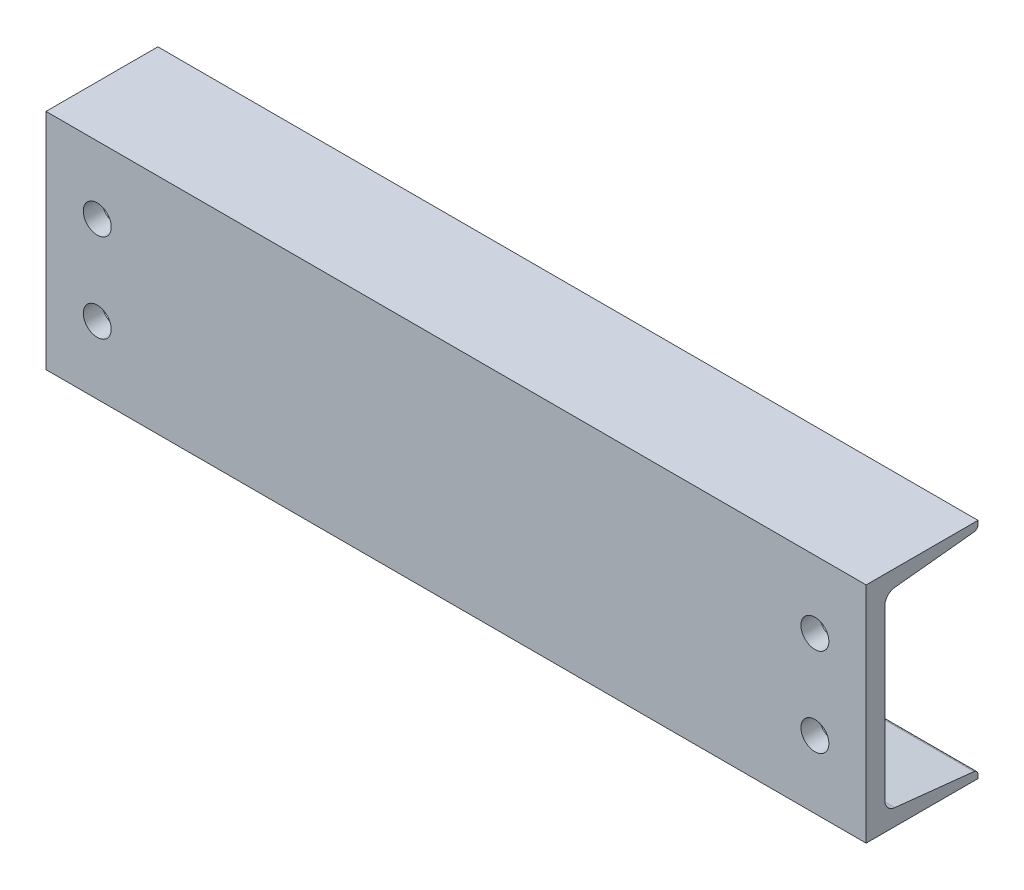
SolidWorks part; units mm, degrees
ref_plane "Front Plane" through (0, 0, 0) normal (0, 0, 1) x (1, 0, 0)
ref_plane "Top Plane" through (0, 0, 0) normal (0, 1, 0) x (1, 0, 0)
ref_plane "Right Plane" through (0, 0, 0) normal (1, 0, 0) x (0, 0, -1)
sketch "Sketch1" plane through (0, 0, 0) normal (1, 0, 0) x (0, 0, -1)
  line L0 (-48.8061, -76.2) -> (-48.8061, 76.2)
  line L1 (-48.8061, 76.2) -> (27.3939, 76.2)
  line L2 (-48.8061, -76.2) -> (27.3939, -76.2)
  line L3 (4.3561, -67.4878) -> (-21.0439, -67.4878) construction
  line L4 (-36.1061, 57.3918) -> (-36.1061, -57.3918)
  line L5 (27.3939, 76.2) -> (27.3939, 73.7107)
  line L6 (27.3939, -76.2) -> (27.3939, -73.7107)
  line L7 (-29.2881, 64.9695) -> (24.6667, 70.6797)
  line L8 (-29.2881, -64.9695) -> (24.6667, -70.6797)
  arc A0 (-36.1061, -57.3918) -> (-29.2881, -64.9695) centre (-28.4861, -57.3918) ccw
  arc A1 (-36.1061, 57.3918) -> (-29.2881, 64.9695) centre (-28.4861, 57.3918) cw
  arc A2 (27.3939, 73.7107) -> (24.6667, 70.6797) centre (24.3459, 73.7107) cw
  arc A3 (27.3939, -73.7107) -> (24.6667, -70.6797) centre (24.3459, -73.7107) ccw
  dimension "D1" = 76.2
  dimension "D2" = 152.4
  dimension "D3" = 12.7
extrude "Boss-Extrude1" add sketch "Sketch1" along normal mid plane 558.8
sketch "Sketch2" plane through (0, 0, 48.8061) normal (0, 0, 1) x (1, 0, 0)
  line L0 (0, 76.2) -> (0, -76.2) construction
  line L1 (279.4, 76.2) -> (-279.4, 76.2) construction
  line L2 (279.4, -76.2) -> (-279.4, -76.2) construction
  line L3 (-279.4, 0) -> (279.4, 0) construction
  line L4 (-279.4, 76.2) -> (-279.4, -76.2) construction
  line L5 (279.4, 76.2) -> (279.4, -76.2) construction
  circle A0 centre (-244.475, 30.1625) radius 9.525
  circle A1 centre (-244.475, -30.1625) radius 9.525
  circle A2 centre (244.475, -30.1625) radius 9.525
  circle A3 centre (244.475, 30.1625) radius 9.525
  dimension "D1" = 19.05
  dimension "D2" = 46.0375
  dimension "D3" = 34.925
extrude "Cut-Extrude1" cut sketch "Sketch2" against normal up to next
sketch "Sketch3" plane through (0, -76.2, 0) normal (0, -1, 0) x (1, 0, 0)
  line L0 (0, 48.8061) -> (0, -27.3939) construction
  line L1 (279.4, 48.8061) -> (-279.4, 48.8061) construction
  line L2 (279.4, -27.3939) -> (-279.4, -27.3939) construction
  line L3 (-279.4, 48.8061) -> (-279.4, -27.3939) construction
  circle A0 centre (-165.1, 10.7061) radius 9.525
  circle A1 centre (165.1, 10.7061) radius 9.525
  dimension "D3" = 19.05
  dimension "D1" = 38.1
  dimension "D2" = 114.3
extrude "Cut-Extrude2" cut sketch "Sketch3" against normal up to next
